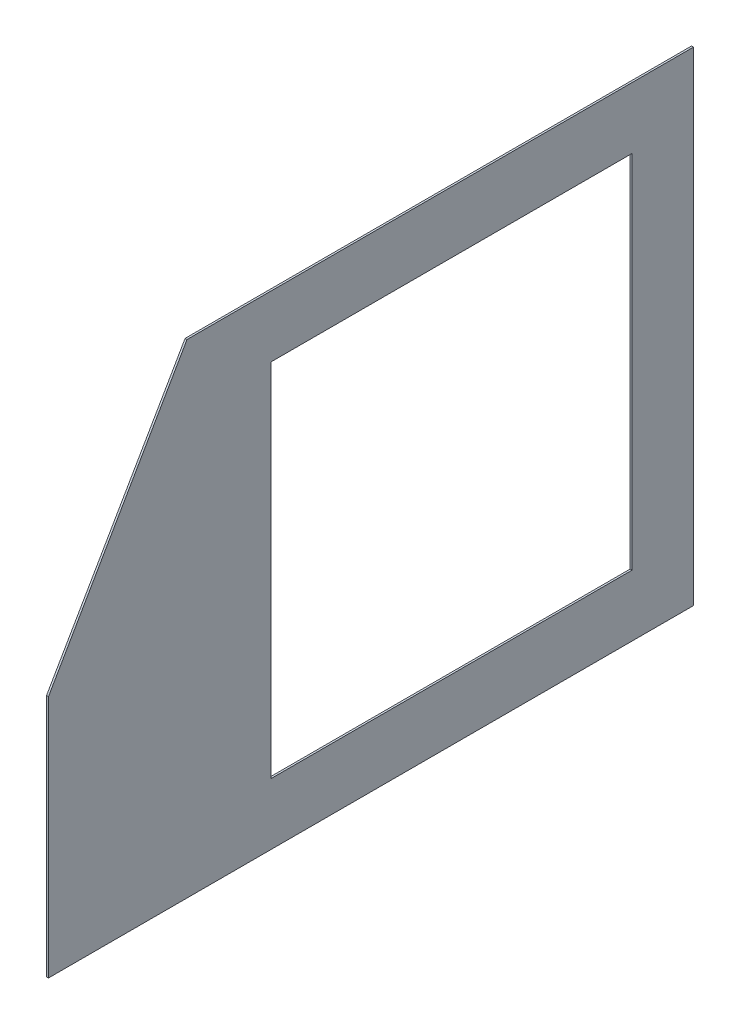
SolidWorks part; units mm, degrees
ref_plane "Front Plane" through (0, 0, 0) normal (0, 0, 1) x (1, 0, 0)
ref_plane "Top Plane" through (0, 0, 0) normal (0, 1, 0) x (1, 0, 0)
ref_plane "Right Plane" through (0, 0, 0) normal (1, 0, 0) x (0, 0, -1)
sketch "Sketch1" plane through (0, 0, 0) normal (1, 0, 0) x (0, 0, -1)
  line L0 (0, 0) -> (-837.6641, 0)
  line L1 (-837.6641, 0) -> (-1066.8, -396.875)
  line L2 (-1066.8, -396.875) -> (-1066.8, -800.1)
  line L3 (-1066.8, -800.1) -> (0, -800.1)
  line L4 (0, -800.1) -> (0, 0)
  dimension "D1" = 800.1
  dimension "D2" = 1066.8
  dimension "D3" = 30
  dimension "D4" = 403.225
  dimension "D5" = 837.6641
extrude "Boss-Extrude1" add sketch "Sketch1" along normal blind 3.175
sketch "Sketch2" plane through (3.175, 0, 0) normal (1, 0, 0) x (0, 0, -1)
  line L2 (-101.6, -396.875) -> (-101.6, -101.6)
  line L3 (-101.6, -101.6) -> (-698.5, -101.6)
  line L4 (0, -800.1) -> (0, 0) construction
  line L7 (-698.5, -101.6) -> (-698.5, -698.5)
  line L8 (-698.5, -698.5) -> (-101.6, -698.5)
  line L9 (-101.6, -698.5) -> (-101.6, -396.875)
  line L10 (-1066.8, -800.1) -> (0, -800.1) construction
  dimension "D1" = 101.6
  dimension "D3" = 596.9
  dimension "D4" = 596.9
  dimension "D5" = 101.6
extrude "Cut-Extrude1" cut sketch "Sketch2" against normal up to next
